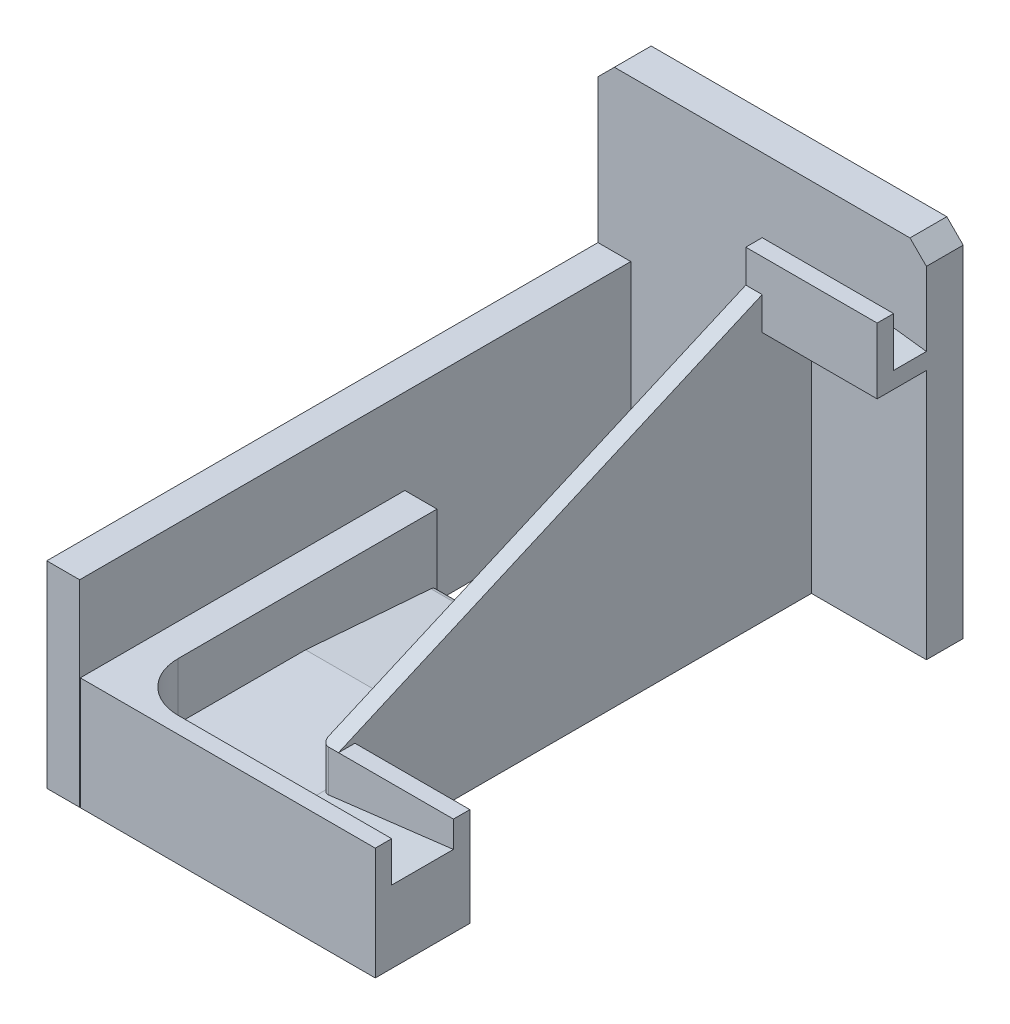
SolidWorks part; units mm, degrees
ref_plane "前视基准面" through (0, 0, 0) normal (0, 0, 1) x (1, 0, 0)
ref_plane "上视基准面" through (0, 0, 0) normal (0, 1, 0) x (1, 0, 0)
ref_plane "右视基准面" through (0, 0, 0) normal (1, 0, 0) x (0, 0, -1)
sketch "草图1" plane through (0, 0, 0) normal (0, 0, 1) x (1, 0, 0)
  line L0 (0, 103.73) -> (5, 108.73)
  line L1 (0, 0) -> (100, 0)
  line L2 (0, 0) -> (0, 103.73)
  line L3 (5, 108.73) -> (95, 108.73)
  line L4 (100, 0) -> (100, 103.73)
  line L5 (95, 108.73) -> (100, 103.73)
  point P1 (100, 108.73)
  point P2 (0, 108.73)
  dimension "D1" = 100
  dimension "D2" = 108.73
extrude "凸台-拉伸1" add sketch "草图1" along normal blind 11.2
ref_plane "基准面1" through (0, 0, 21.2) normal (0, 0, 1) x (1, 0, 0)
sketch "草图3" plane through (0, 0, 21.2) normal (0, 0, 1) x (1, 0, 0)
  line L0 (100, 0) -> (100, 103.73) construction
  line L1 (100, 76.29) -> (60, 76.29)
  line L2 (100, 76.29) -> (100, 96.29)
  line L3 (100, 96.29) -> (60, 96.29)
  line L4 (60, 76.29) -> (60, 96.29)
  line L5 (0, 0) -> (100, 0) construction
  dimension "D1" = 40
  dimension "D2" = 20
  dimension "D3" = 96.29
extrude "凸台-拉伸2" add sketch "草图3" along normal blind 5 separate body
sketch "草图5" plane through (0, 0, 21.2) normal (0, 0, -1) x (-1, 0, 0)
  line L0 (-60, 86.29) -> (-100, 81.29)
  line L1 (-60, 96.29) -> (-60, 76.29) construction
  line L2 (-100, 76.29) -> (-100, 96.29) construction
  line L3 (-60, 86.29) -> (-60, 76.29)
  line L4 (-60, 76.29) -> (-100, 76.29)
  line L5 (-100, 76.29) -> (-100, 81.29)
  dimension "D1" = 10
  dimension "D2" = 5
extrude "凸台-拉伸3" add sketch "草图5" along normal up to next (10 mm away)
sketch "草图6" plane through (60, 0, 0) normal (-1, 0, 0) x (0, 0, 1)
  line L0 (26.2, 86.29) -> (155.2, 30)
  line L1 (26.2, 96.29) -> (26.2, 76.29) construction
  line L2 (155.2, 30) -> (155.2, 0)
  line L3 (155.2, 0) -> (26.2, 0)
  line L4 (26.2, 76.29) -> (26.2, 86.29)
  line L5 (26.2, 76.29) -> (11.2, 76.29)
  line L6 (11.2, 76.29) -> (11.2, 0)
  line L7 (11.2, 0) -> (26.2, 0)
  dimension "D1" = 30
  dimension "D2" = 129
extrude "凸台-拉伸4" add sketch "草图6" against normal blind 5
ref_plane "基准面2" through (10.2, 0, 0) normal (-1, 0, 0) x (0, 0, 1)
sketch "草图7" plane through (10.2, 0, 0) normal (-1, 0, 0) x (0, 0, 1)
  line L0 (11.2, 0) -> (155.2, 0) construction
  line L1 (80.2, 0) -> (179, 0)
  line L2 (80.2, 0) -> (80.2, 34.24)
  line L3 (80.2, 34.24) -> (179, 34.24)
  line L4 (179, 0) -> (179, 34.24)
  dimension "D1" = 98.8
  dimension "D2" = 34.24
  dimension "D3" = 80.2
extrude "凸台-拉伸5" add sketch "草图7" against normal blind 9.8 separate body
sketch "草图8" plane through (0, 0, 179) normal (0, 0, 1) x (1, 0, 0)
  line L0 (100, 0) -> (100, 76.29) construction
  line L1 (20, 0) -> (100, 0)
  line L2 (20, 0) -> (20, 34.24)
  line L3 (20, 34.24) -> (100, 34.24)
  line L4 (100, 0) -> (100, 34.24)
  line L8 (20, 34.24) -> (10.2, 34.24) construction
extrude "凸台-拉伸6" add sketch "草图8" against normal blind 5
sketch "草图9" plane through (0, 0, 155.2) normal (0, 0, 1) x (1, 0, 0)
  line L0 (65, 30) -> (60, 30) construction
  line L1 (65, 0) -> (100, 0)
  line L2 (65, 0) -> (65, 30)
  line L3 (65, 30) -> (100, 30)
  line L4 (100, 0) -> (100, 30)
  line L8 (100, 0) -> (100, 34.24) construction
  point P5 (100, 34.24)
extrude "凸台-拉伸7" add sketch "草图9" against normal blind 5
sketch "草图11" plane through (20, 0, 0) normal (1, 0, 0) x (0, 0, -1)
  line L0 (-80.2, 0) -> (-80.2, 14)
  line L1 (-80.2, 34.24) -> (-80.2, 0) construction
  line L2 (-80.2, 14) -> (-120.2, 17.12)
  line L3 (-120.2, 17.12) -> (-174, 17.12)
  line L5 (-174, 0) -> (-174, 34.24) construction
  line L6 (-174, 17.12) -> (-174, 0)
  line L7 (-174, 0) -> (-80.2, 0)
  point P6 (0, 0)
  dimension "D1" = 14
  dimension "D2" = 40
extrude "凸台-拉伸8" add sketch "草图11" along normal up to surface (40 mm away) up to face at (60, 60.1812, 53.45)
fillet "圆角1" radius 2 1 edges at (40, 14, 80.2)
sketch "草图12" plane through (0, 0, 155.2) normal (0, 0, 1) x (1, 0, 0)
  line L0 (60, 0) -> (60, 17.12)
  line L1 (60, 17.12) -> (100, 22)
  line L2 (100, 0) -> (100, 30) construction
  line L3 (100, 22) -> (100, 0)
  line L4 (100, 0) -> (60, 0)
  dimension "D1" = 22
extrude "凸台-拉伸9" add sketch "草图12" along normal up to next
sketch "草图14" plane through (0, 0, 11.2) normal (0, 0, 1) x (1, 0, 0)
  line L1 (0, 0) -> (10, 0)
  line L2 (0, 0) -> (0, 60)
  line L3 (0, 60) -> (10, 60)
  line L4 (10, 0) -> (10, 60)
  dimension "D1" = 10
  dimension "D2" = 60
extrude "凸台-拉伸12" add sketch "草图14" along normal up to surface (167.8 mm away) up to face at (55.1, 17.12, 179)
sketch "草图15" plane through (0, 17.12, 0) normal (0, 1, 0) x (1, 0, 0)
  line L0 (20, -120.2) -> (20, -174) construction
  line L1 (100, -174) -> (20, -174) construction
  line L2 (20, -159) -> (20, -174)
  line L3 (20, -174) -> (35, -174)
  arc A0 (20, -159) -> (35, -174) centre (35, -159) ccw
  dimension "D1" = 15
extrude "凸台-拉伸13" add sketch "草图15" along normal up to surface (17.12 mm away) up to face at (43.4, 34.24, 144.4)
fillet "圆角3" radius 2 1 edges at (60, 23.56, 155.2)
